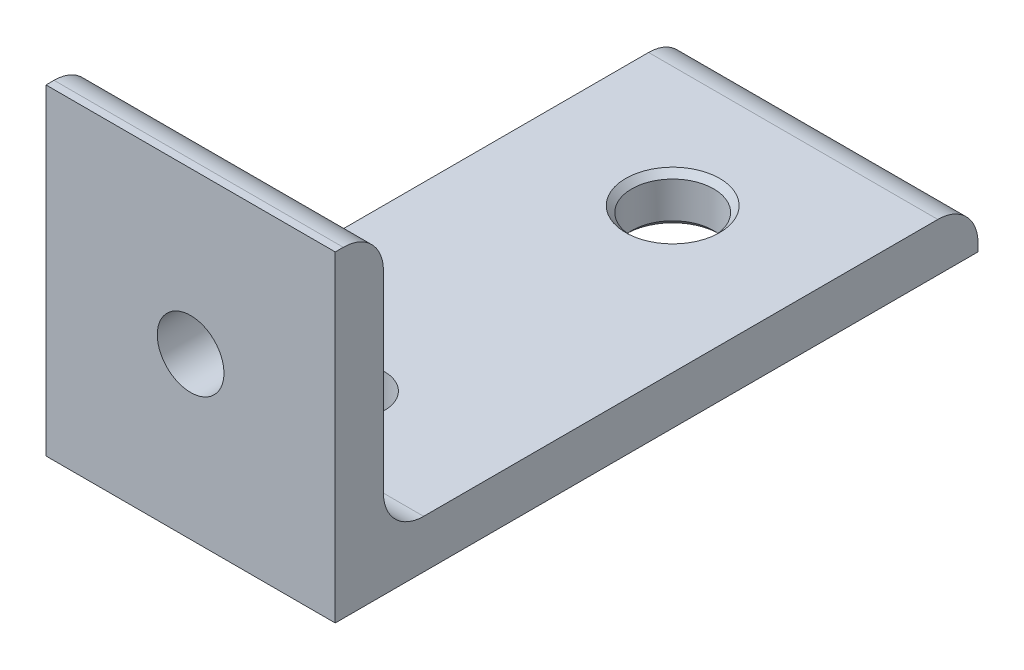
SolidWorks part; units mm, degrees
ref_plane "Front Plane" through (0, 0, 0) normal (0, 0, 1) x (1, 0, 0)
ref_plane "Top Plane" through (0, 0, 0) normal (0, 1, 0) x (1, 0, 0)
ref_plane "Right Plane" through (0, 0, 0) normal (1, 0, 0) x (0, 0, -1)
sketch "Sketch1" plane through (0, 0, 0) normal (1, 0, 0) x (0, 0, -1)
  line L0 (0, 40) -> (0, 0)
  line L1 (0, 0) -> (80, 0)
  line L2 (6, 40) -> (6, 6)
  line L3 (6, 6) -> (80, 6)
  line L4 (0, 40) -> (6, 40)
  line L5 (80, 6) -> (80, 0)
  dimension "D1" = 40
  dimension "D2" = 6
  dimension "D3" = 80
extrude "Boss-Extrude1" add sketch "Sketch1" along normal mid plane 36
sketch "Sketch2" plane through (0, 6, 0) normal (0, 1, 0) x (1, 0, 0)
  circle A0 centre (0, 20) radius 4.15
  circle A1 centre (0, 60) radius 5.1
  dimension "D1" = 8.3
  dimension "D3" = 10.2
  dimension "D2" = 20
  dimension "D4" = 40
extrude "Cut-Extrude1" cut sketch "Sketch2" against normal through all contours A1 | A0
sketch "Sketch3" plane through (0, 0, -6) normal (0, 0, -1) x (-1, 0, 0)
  circle A0 centre (0, 20) radius 4.15
  dimension "D1" = 8.3
  dimension "D2" = 20
extrude "Cut-Extrude2" cut sketch "Sketch3" against normal through all
fillet "Fillet1" radius 5 3 edges at (0, 40, -6) (0, 6, -80) (0, 6, -6)
chamfer "Chamfer1" distance 0.75 angle 45 2 edges at (0, 0, -54.9) (0, 6, -54.9)
